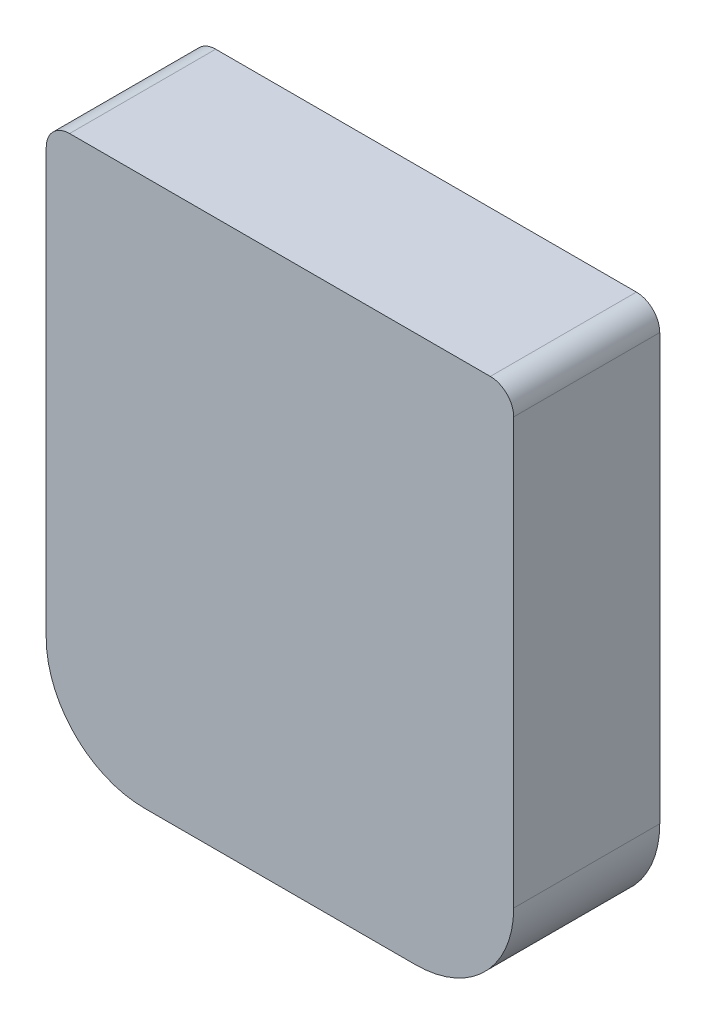
SolidWorks part; units mm, degrees
material "6061 Alloy"
ref_plane "Front Plane" through (0, 0, 0) normal (0, 0, 1) x (1, 0, 0)
ref_plane "Top Plane" through (0, 0, 0) normal (0, 1, 0) x (1, 0, 0)
ref_plane "Right Plane" through (0, 0, 0) normal (1, 0, 0) x (0, 0, -1)
sketch "Sketch1" plane through (0, 0, 0) normal (0, 0, 1) x (1, 0, 0)
  line L0 (-5, 4.9) -> (5, 4.9)
  line L1 (-5, 4.9) -> (-5, -6.8)
  line L2 (5, 4.9) -> (5, -6.8)
  line L3 (-5, -6.8) -> (5, -6.8)
  line L4 (0, 4.9) -> (0, 0) construction
  line L5 (0, 0) -> (0, -6.8) construction
  dimension "D1" = 10
  dimension "D2" = 4.9
  dimension "D3" = 6.8
extrude "Boss-Extrude1" add sketch "Sketch1" along normal blind 3.125
fillet "Fillet1" radius 2.1 2 edges at (5, -6.8, 1.5625) (-5, -6.8, 1.5625)
fillet "Fillet2" radius 0.5 2 edges at (5, 4.9, 1.5625) (-5, 4.9, 1.5625)
